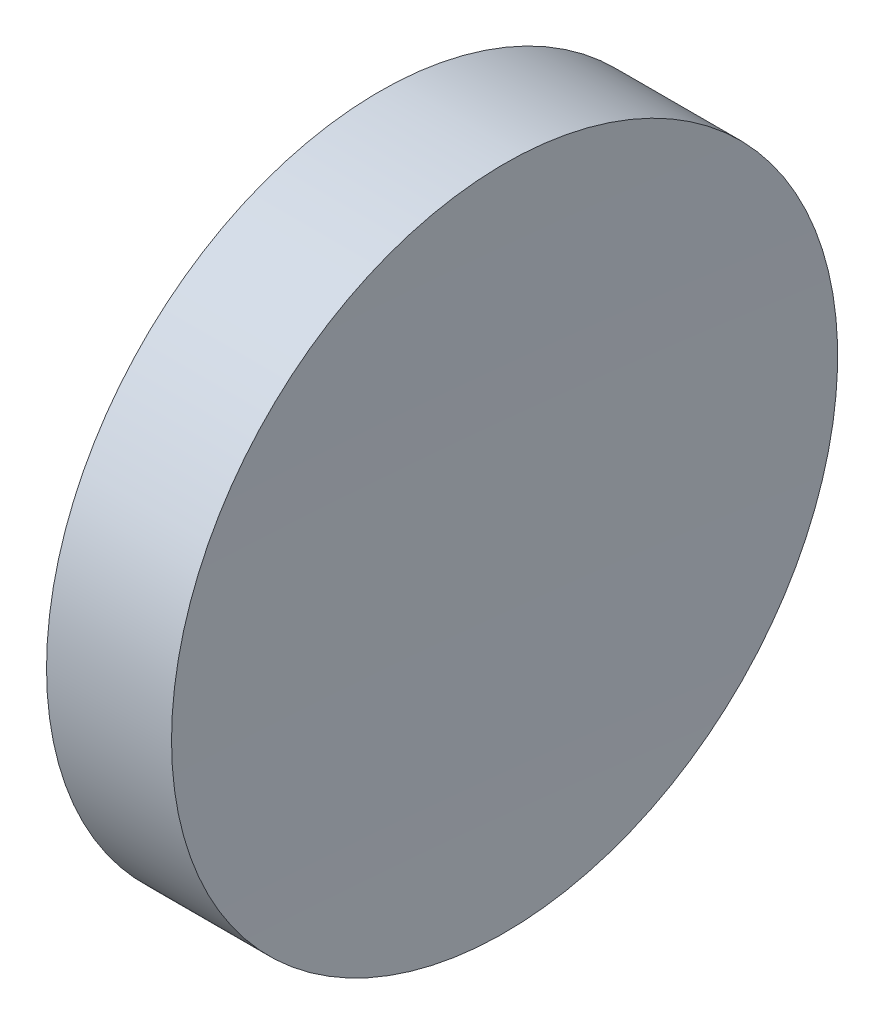
SolidWorks part; units mm, degrees
ref_plane "前视基准面" through (0, 0, 0) normal (0, 0, 1) x (1, 0, 0)
ref_plane "上视基准面" through (0, 0, 0) normal (0, 1, 0) x (1, 0, 0)
ref_plane "右视基准面" through (0, 0, 0) normal (1, 0, 0) x (0, 0, -1)
sketch "草图1" plane through (0, 0, 0) normal (0, 1, 0) x (1, 0, 0)
  line L0 (0, 0) -> (6.9328, 0) construction
  line L1 (0, 0) -> (9.21, 0)
  line L2 (0, 0) -> (0, 25.4)
  line L3 (0, 25.4) -> (9.5326, 25.4)
  arc A0 (9.5326, 25.4) -> (9.21, 0) centre (1009.21, 0) ccw
  dimension "D3" = 1000
  dimension "D1" = 9.21
  dimension "D2" = 25.4
revolve "旋转1" add sketch "草图1" angle 360 about L0
